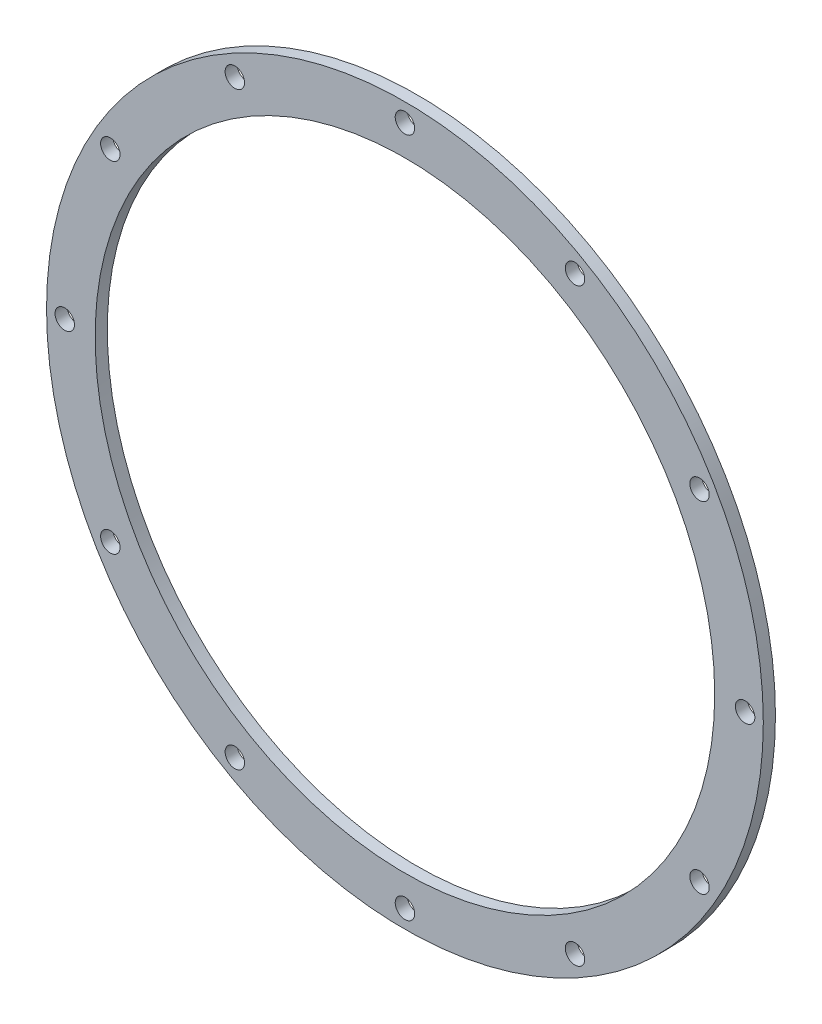
SolidWorks part; units mm, degrees
material "AISI 304"
ref_plane "前视基准面" through (0, 0, 0) normal (0, 0, 1) x (1, 0, 0)
ref_plane "上视基准面" through (0, 0, 0) normal (0, 1, 0) x (1, 0, 0)
ref_plane "右视基准面" through (0, 0, 0) normal (1, 0, 0) x (0, 0, -1)
sketch "草图1" plane through (0, 0, 0) normal (0, 0, 1) x (1, 0, 0)
  circle A0 centre (0, 0) radius 59
  circle A1 centre (0, 0) radius 51
  circle A2 centre (0, 0) radius 56 construction
  circle A3 centre (0, 56) radius 1.6
  circle A4 centre (28, 48.4974) radius 1.6
  circle A5 centre (48.4974, 28) radius 1.6
  circle A6 centre (56, 0) radius 1.6
  circle A7 centre (48.4974, -28) radius 1.6
  circle A8 centre (28, -48.4974) radius 1.6
  circle A9 centre (0, -56) radius 1.6
  circle A10 centre (-28, -48.4974) radius 1.6
  circle A11 centre (-48.4974, -28) radius 1.6
  circle A12 centre (-56, 0) radius 1.6
  circle A13 centre (-48.4974, 28) radius 1.6
  circle A14 centre (-28, 48.4974) radius 1.6
  point P31 (0, 0)
  dimension "D1" = 118
  dimension "D2" = 102
  dimension "D3" = 3
  dimension "D4" = 3.2
  dimension "D5" = 12
extrude "凸台-拉伸1" add sketch "草图1" along normal blind 2
